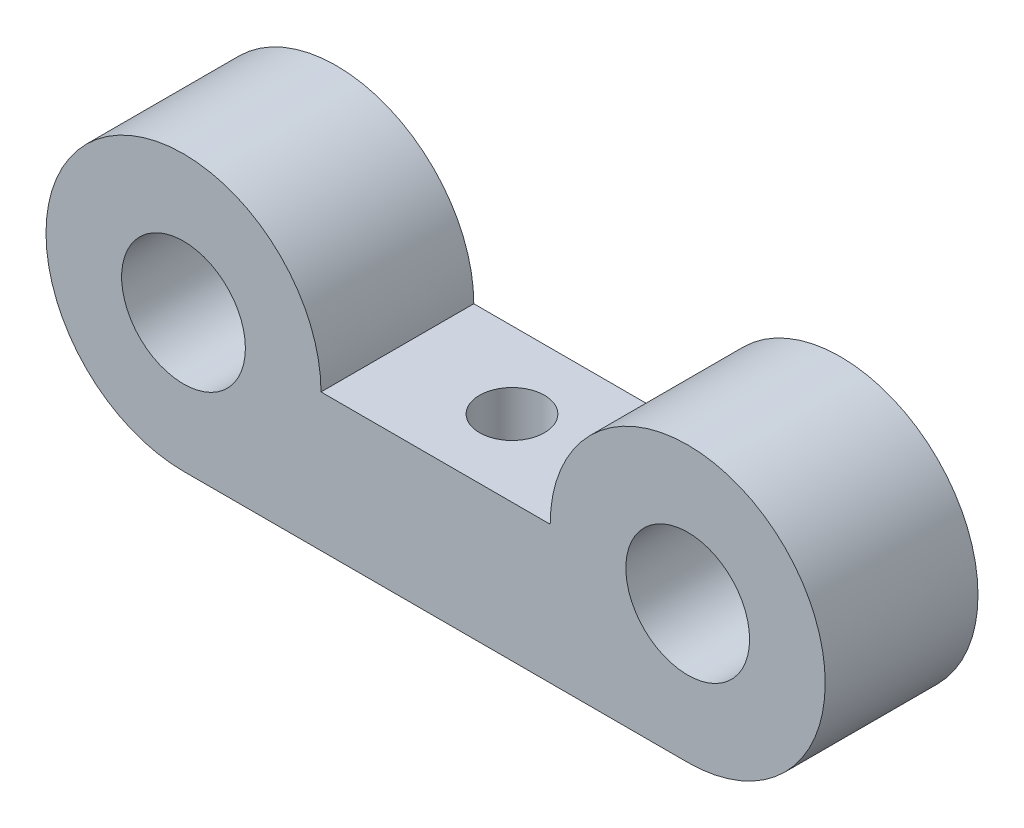
SolidWorks part; units mm, degrees
material "ABS"
ref_plane "Plano frontal" through (0, 0, 0) normal (0, 0, 1) x (1, 0, 0)
ref_plane "Plano superior" through (0, 0, 0) normal (0, 1, 0) x (1, 0, 0)
ref_plane "Plano direito" through (0, 0, 0) normal (1, 0, 0) x (0, 0, -1)
sketch "Esboço1" plane through (0, 0, 0) normal (0, 0, 1) x (1, 0, 0)
  line L0 (-16.5, 0) -> (16.5, 0) construction
  line L1 (-16.5, 0) -> (16.5, 0) construction
  line L3 (-16.5, -9) -> (16.5, -9)
  line L4 (0, 0) -> (0, 11.918) construction
  line L10 (-7.5, 0) -> (7.5, 0)
  circle A0 centre (-16.5, 0) radius 4.05
  circle A1 centre (16.5, 0) radius 4.05
  arc A2 (-7.5, 0) -> (-16.5, -9) centre (-16.5, 0) ccw
  arc A3 (16.5, -9) -> (7.5, 0) centre (16.5, 0) ccw
  point P4 (0, 0)
  point P6 (0, 0)
  dimension "D2" = 8.1
  dimension "D3" = 9
  dimension "D1" = 33
extrude "Ressalto-extrusão1" add sketch "Esboço1" along normal blind 10
sketch "Esboço2" plane through (0, 0, 0) normal (0, 1, 0) x (1, 0, 0)
  line L0 (7.5, -5) -> (-7.5, -5) construction
  line L1 (7.5, -10) -> (7.5, 0) construction
  line L2 (-7.5, -10) -> (-7.5, 0) construction
  circle A0 centre (0, -5) radius 2.125
extrude "Corte-extrusão1" cut sketch "Esboço2" against normal blind 10 contours A0
